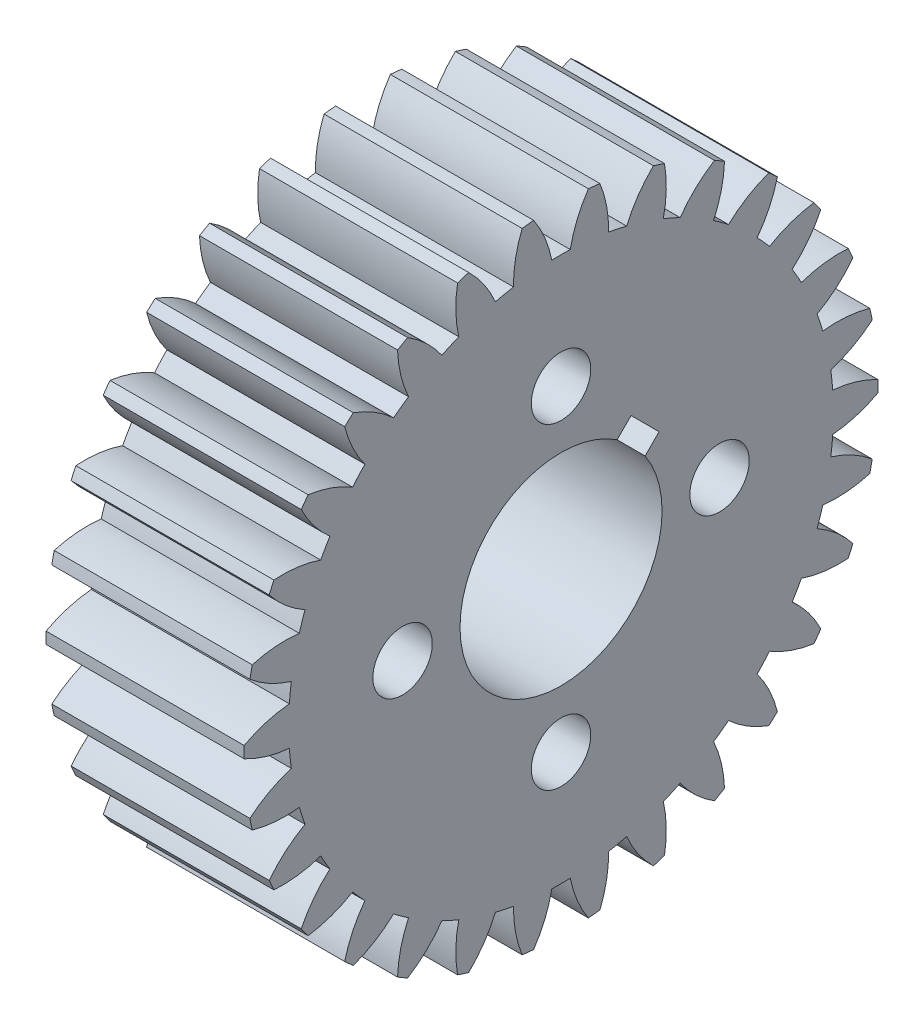
SolidWorks part; units mm, degrees
ref_plane "Plane1" through (0, 0, 0) normal (0, 0, 1) x (1, 0, 0)
ref_plane "Plane2" through (0, 0, 0) normal (0, 1, 0) x (1, 0, 0)
ref_plane "Plane3" through (0, 0, 0) normal (1, 0, 0) x (0, 0, -1)
sketch "HoldingSke" plane through (0, 0, 0) normal (0, 1, 0) x (1, 0, 0)
  line L0 (0, 0) -> (0.866, -0.5)
  line L1 (-15, 0) -> (100, 0) construction
  line L2 (0, 0) -> (-2.1039, 2.3779)
  line L3 (0, 0) -> (-11.863, 4.5341)
  line L4 (0, 0) -> (7.479, 4.318)
  line L5 (0, 0) -> (-16.8652, -6.2902)
  line L6 (0, 0) -> (-8.2896, -5.593)
  line L7 (-2.1039, 2.3779) -> (1.7706, 19.956)
  line L8 (-76.2, 54.61) -> (-75.2, 54.61)
  line L9 (-71.009, 38.7566) -> (-53.1078, 45.2721)
  line L10 (-76.2, 71.12) -> (104.1128, 71.12)
  line L11 (0, 0) -> (-10, 0)
  line L12 (-76.2, 101.6) -> (-76.162, 101.6)
  line L13 (24.9733, 27.94) -> (52.9518, 28.4284)
  line L14 (24.9733, 27.94) -> (24.9743, 27.94)
  line L15 (24.9733, 27.94) -> (100.4006, 29.5858)
  line L16 (-63.627, -1) -> (-12.827, -1)
  circle A0 centre (0, 0) radius 3
  circle A1 centre (0, 0) radius 12.5
  circle A2 centre (0, 0) radius 12.5
  circle A3 centre (0, 0) radius 3
  dimension "MHD" = 25
  dimension "Hub_dia" = 25
  dimension "Bore" = 6
  dimension "MBD" = 6
  dimension "Num_teeth" = 30
  dimension "Pitch" = 1
  dimension "Overall_len" = 18
  dimension "Show_teeth" = 30
  dimension "Thickness" = 10
  dimension "OAL" = 18.0001
  dimension "T_dim" = 1
  dimension "Ap" = 20
  dimension "H" = 19.05
  dimension "Pitch_radius" = 180.3128
  dimension "Width" = 10
  dimension "Backlash" = 0.038
  dimension "Addendum_fac" = 1
  dimension "Dedendum_fac" = 1.25
  dimension "Clearance_fac" = 0.25
  dimension "Dedendum_add" = 0.001
  dimension "Module" = 1
sketch "BasProSke" plane through (0, 0, 0) normal (0, 1, 0) x (1, 0, 0)
  line L0 (-10, 0) -> (60, 0) construction
  line L1 (0, 0) -> (0, 16)
  line L2 (0, 0) -> (10, 0)
  line L3 (10, 0) -> (10, 16)
  line L4 (10, 16) -> (0, 16)
  dimension "Thickness" = 10
  dimension "Diameter" = 32
revolve "Base-Revolve" add sketch "BasProSke" angle 360 about L0
sketch "TooCutSke" plane through (0, 0, 0) normal (1, 0, 0) x (0, 0, -1)
  line L1 (0, 0) -> (0, 107) construction
  line L2 (0, 0) -> (-0.8515, 14.9758) construction
  line L3 (0, 0) -> (-3.1323, 29.8014) construction
  line L4 (-0.8515, 14.9758) -> (-1.5661, 14.9007) construction
  arc A0 (0.4664, 13.7411) -> (-0.4664, 13.7411) centre (0, 0) ccw
  arc A1 (1.3975, 15.9644) -> (-1.3975, 15.9644) centre (0, 0) ccw
  circle A2 centre (0, 0) radius 15 construction
  circle A3 centre (0, 0) radius 14.0954 construction
  arc A4 (-0.4664, 13.7411) -> (-1.3975, 15.9644) centre (-6.3534, 12.5823) ccw
  arc A5 (1.3975, 15.9644) -> (0.4664, 13.7411) centre (6.3534, 12.5823) ccw
  dimension "Root_dia" = 27.498
  dimension "Overcut_dia" = 32.0508
  dimension "Pitch_dia" = 30
  dimension "Base_dia" = 28.1908
  dimension "Flank_rad" = 6
  dimension "Half_ang" = 6
  dimension "Half_CT" = 0.7185
extrude "ToothCut" cut sketch "TooCutSke" along normal through all
fillet "Breaks" [suppressed] radius 0.02
fillet "RootFillets" [suppressed] radius 0.251
pattern_circular "TeethCuts" count 30 every 12 about axis through (-10, 0, 0) along (1, 0, 0) of "ToothCut", "RootFillets", "Breaks"
sketch "HubNeaOneSke" plane through (0, 0, 0) normal (-1, 0, 0) x (0, 0, 1)
  circle A0 centre (0, 0) radius 12.5
  dimension "Diameter" = 25
extrude "HubNearOne" add sketch "HubNeaOneSke" along normal blind 8.0001
sketch "HubNeaBotSke" plane through (0, 0, 0) normal (-1, 0, 0) x (0, 0, 1)
  circle A0 centre (0, 0) radius 12.5
  dimension "Diameter" = 25
extrude "HubNearBoth" [suppressed] add sketch "HubNeaBotSke" along normal blind 4
ref_plane "FarPln" through (10, 0, 0) normal (1, 0, 0) x (0, 0, -1)
sketch "HubFarSke" plane through (10, 0, 0) normal (1, 0, 0) x (0, 0, -1)
  circle A0 centre (0, 0) radius 12.5
  dimension "Diameter" = 25
extrude "HubFar" [suppressed] add sketch "HubFarSke" along normal blind 4
sketch "BorSke" plane through (0, 0, 0) normal (1, 0, 0) x (0, 0, -1)
  circle A0 centre (0, 0) radius 3
  dimension "Diameter" = 6
extrude "Bore" cut sketch "BorSke" along normal mid plane 36.0001
sketch "KeySke" plane through (0, 0, 0) normal (1, 0, 0) x (0, 0, -1)
  line L0 (-1, 0) -> (-1, 4)
  line L1 (-1, 4) -> (1, 4)
  line L2 (1, 4) -> (1, 0)
  line L3 (0, 0) -> (0, 34) construction
  line L4 (-1, 0) -> (1, 0)
  dimension "Offset" = 4
  dimension "Width" = 2
extrude "Keyway" [suppressed] cut sketch "KeySke" along normal mid plane 36.0001
pattern_circular "Keyway2" [suppressed] count 2 every 90 about axis through (-10, 0, 0) along (1, 0, 0)
sketch "Sketch2" plane through (-8.0001, 0, 0) normal (-1, 0, 0) x (0, 0, 1)
  circle A1 centre (0, 0) radius 12.5
  circle A2 centre (0, 0) radius 12.5
  dimension "D1" = 0
extrude "Cut-Extrude1" cut sketch "Sketch2" against normal up to surface (8.0001 mm away) up to face at (0, 0, -12.5)
sketch "Sketch3" plane through (10, 0, 0) normal (1, 0, 0) x (0, 0, -1)
  circle A0 centre (0, 0) radius 5.1
  arc A120 (-15.9973, -0.2927) -> (-13.7146, -0.9725) centre (-13.1775, 5.0034) ccw
  arc A121 (-13.7146, -0.9725) -> (-13.6171, -1.9002) centre (0, 0) ccw
  arc A122 (-13.6171, -1.9002) -> (-15.7086, -3.0398) centre (-11.8492, -7.6338) ccw
  arc A123 (-15.7086, -3.0398) -> (-15.5869, -3.6123) centre (0, 0) ccw
  arc A124 (-15.5869, -3.6123) -> (-13.2127, -3.8027) centre (-13.9298, 2.1543) ccw
  arc A125 (-13.2127, -3.8027) -> (-12.9244, -4.6898) centre (0, 0) ccw
  arc A126 (-12.9244, -4.6898) -> (-14.7333, -6.2393) centre (-10.0031, -9.9306) ccw
  arc A127 (-14.7333, -6.2393) -> (-14.4952, -6.7741) centre (0, 0) ccw
  arc A128 (-14.4952, -6.7741) -> (-12.1333, -6.4666) centre (-14.0733, -0.7889) ccw
  arc A129 (-12.1333, -6.4666) -> (-11.6669, -7.2745) centre (0, 0) ccw
  arc A130 (-11.6669, -7.2745) -> (-13.1141, -9.1662) centre (-7.7199, -11.7934) ccw
  arc A131 (-13.1141, -9.1662) -> (-12.7701, -9.6398) centre (0, 0) ccw
  arc A132 (-12.7701, -9.6398) -> (-10.5237, -8.848) centre (-13.6017, -3.6977) ccw
  arc A133 (-10.5237, -8.848) -> (-9.8995, -9.5412) centre (0, 0) ccw
  arc A134 (-9.8995, -9.5412) -> (-10.9218, -11.6925) centre (-5.0992, -13.1407) ccw
  arc A135 (-10.9218, -11.6925) -> (-10.4868, -12.0842) centre (0, 0) ccw
  arc A136 (-10.4868, -12.0842) -> (-8.4541, -10.8426) centre (-12.5357, -6.4448) ccw
  arc A137 (-8.4541, -10.8426) -> (-7.6995, -11.3909) centre (0, 0) ccw
  arc A138 (-7.6995, -11.3909) -> (-8.2521, -13.7078) centre (-2.2556, -13.9137) ccw
  arc A139 (-8.2521, -13.7078) -> (-7.7452, -14.0004) centre (0, 0) ccw
  arc A140 (-7.7452, -14.0004) -> (-6.0151, -12.3634) centre (-10.9218, -8.9103) ccw
  arc A141 (-6.0151, -12.3634) -> (-5.1629, -12.7428) centre (0, 0) ccw
  arc A142 (-5.1629, -12.7428) -> (-5.2218, -15.1239) centre (0.6865, -14.0787) ccw
  arc A143 (-5.2218, -15.1239) -> (-4.6651, -15.3048) centre (0, 0) ccw
  arc A144 (-4.6651, -15.3048) -> (-3.3131, -13.3438) centre (-8.8306, -10.9864) ccw
  arc A145 (-3.3131, -13.3438) -> (-2.4007, -13.5378) centre (0, 0) ccw
  arc A146 (-2.4007, -13.5378) -> (-1.9632, -15.8791) centre (3.5986, -13.6283) ccw
  arc A147 (-1.9632, -15.8791) -> (-1.3811, -15.9403) centre (0, 0) ccw
  arc A148 (-1.3811, -15.9403) -> (-0.4664, -13.7411) centre (-6.3534, -12.5823) ccw
  arc A149 (-0.4664, -13.7411) -> (0.4664, -13.7411) centre (0, 0) ccw
  arc A150 (0.4664, -13.7411) -> (1.3811, -15.9403) centre (6.3534, -12.5823) ccw
  arc A151 (1.3811, -15.9403) -> (1.9632, -15.8791) centre (0, 0) ccw
  arc A152 (1.9632, -15.8791) -> (2.4007, -13.5378) centre (-3.5986, -13.6283) ccw
  arc A153 (2.4007, -13.5378) -> (3.3131, -13.3438) centre (0, 0) ccw
  arc A154 (3.3131, -13.3438) -> (4.6651, -15.3048) centre (8.8306, -10.9864) ccw
  arc A155 (4.6651, -15.3048) -> (5.2218, -15.1239) centre (0, 0) ccw
  arc A156 (5.2218, -15.1239) -> (5.1629, -12.7428) centre (-0.6865, -14.0787) ccw
  arc A157 (5.1629, -12.7428) -> (6.0151, -12.3634) centre (0, 0) ccw
  arc A158 (6.0151, -12.3634) -> (7.7452, -14.0004) centre (10.9218, -8.9103) ccw
  arc A159 (7.7452, -14.0004) -> (8.2521, -13.7078) centre (0, 0) ccw
  arc A160 (8.2521, -13.7078) -> (7.6995, -11.3909) centre (2.2556, -13.9137) ccw
  arc A161 (7.6995, -11.3909) -> (8.4541, -10.8426) centre (0, 0) ccw
  arc A162 (8.4541, -10.8426) -> (10.4868, -12.0842) centre (12.5357, -6.4448) ccw
  arc A163 (10.4868, -12.0842) -> (10.9218, -11.6925) centre (0, 0) ccw
  arc A164 (10.9218, -11.6925) -> (9.8995, -9.5412) centre (5.0992, -13.1407) ccw
  arc A165 (9.8995, -9.5412) -> (10.5237, -8.848) centre (0, 0) ccw
  arc A166 (10.5237, -8.848) -> (12.7701, -9.6398) centre (13.6017, -3.6977) ccw
  arc A167 (12.7701, -9.6398) -> (13.1141, -9.1662) centre (0, 0) ccw
  arc A168 (13.1141, -9.1662) -> (11.6669, -7.2745) centre (7.7199, -11.7934) ccw
  arc A169 (11.6669, -7.2745) -> (12.1333, -6.4666) centre (0, 0) ccw
  arc A170 (12.1333, -6.4666) -> (14.4952, -6.7741) centre (14.0733, -0.7889) ccw
  arc A171 (14.4952, -6.7741) -> (14.7333, -6.2393) centre (0, 0) ccw
  arc A172 (14.7333, -6.2393) -> (12.9244, -4.6898) centre (10.0031, -9.9306) ccw
  arc A173 (12.9244, -4.6898) -> (13.2127, -3.8027) centre (0, 0) ccw
  arc A174 (13.2127, -3.8027) -> (15.5869, -3.6123) centre (13.9298, 2.1543) ccw
  arc A175 (15.5869, -3.6123) -> (15.7086, -3.0398) centre (0, 0) ccw
  arc A176 (15.7086, -3.0398) -> (13.6171, -1.9002) centre (11.8492, -7.6338) ccw
  arc A177 (13.6171, -1.9002) -> (13.7146, -0.9725) centre (0, 0) ccw
  arc A178 (13.7146, -0.9725) -> (15.9973, -0.2927) centre (13.1775, 5.0034) ccw
  arc A179 (15.9973, -0.2927) -> (15.9973, 0.2927) centre (0, 0) ccw
  arc A180 (15.9973, 0.2927) -> (13.7146, 0.9725) centre (13.1775, -5.0034) ccw
  arc A181 (13.7146, 0.9725) -> (13.6171, 1.9002) centre (0, 0) ccw
  arc A182 (13.6171, 1.9002) -> (15.7086, 3.0398) centre (11.8492, 7.6338) ccw
  arc A183 (15.7086, 3.0398) -> (15.5869, 3.6123) centre (0, 0) ccw
  arc A184 (15.5869, 3.6123) -> (13.2127, 3.8027) centre (13.9298, -2.1543) ccw
  arc A185 (13.2127, 3.8027) -> (12.9244, 4.6898) centre (0, 0) ccw
  arc A186 (12.9244, 4.6898) -> (14.7333, 6.2393) centre (10.0031, 9.9306) ccw
  arc A187 (14.7333, 6.2393) -> (14.4952, 6.7741) centre (0, 0) ccw
  arc A188 (14.4952, 6.7741) -> (12.1333, 6.4666) centre (14.0733, 0.7889) ccw
  arc A189 (12.1333, 6.4666) -> (11.6669, 7.2745) centre (0, 0) ccw
  arc A190 (11.6669, 7.2745) -> (13.1141, 9.1662) centre (7.7199, 11.7934) ccw
  arc A191 (13.1141, 9.1662) -> (12.7701, 9.6398) centre (0, 0) ccw
  arc A192 (12.7701, 9.6398) -> (10.5237, 8.848) centre (13.6017, 3.6977) ccw
  arc A193 (10.5237, 8.848) -> (9.8995, 9.5412) centre (0, 0) ccw
  arc A194 (9.8995, 9.5412) -> (10.9218, 11.6925) centre (5.0992, 13.1407) ccw
  arc A195 (10.9218, 11.6925) -> (10.4868, 12.0842) centre (0, 0) ccw
  arc A196 (10.4868, 12.0842) -> (8.4541, 10.8426) centre (12.5357, 6.4448) ccw
  arc A197 (8.4541, 10.8426) -> (7.6995, 11.3909) centre (0, 0) ccw
  arc A198 (7.6995, 11.3909) -> (8.2521, 13.7078) centre (2.2556, 13.9137) ccw
  arc A199 (8.2521, 13.7078) -> (7.7452, 14.0004) centre (0, 0) ccw
  arc A200 (7.7452, 14.0004) -> (6.0151, 12.3634) centre (10.9218, 8.9103) ccw
  arc A201 (6.0151, 12.3634) -> (5.1629, 12.7428) centre (0, 0) ccw
  arc A202 (5.1629, 12.7428) -> (5.2218, 15.1239) centre (-0.6865, 14.0787) ccw
  arc A203 (5.2218, 15.1239) -> (4.6651, 15.3048) centre (0, 0) ccw
  arc A204 (4.6651, 15.3048) -> (3.3131, 13.3438) centre (8.8306, 10.9864) ccw
  arc A205 (3.3131, 13.3438) -> (2.4007, 13.5378) centre (0, 0) ccw
  arc A206 (2.4007, 13.5378) -> (1.9632, 15.8791) centre (-3.5986, 13.6283) ccw
  arc A207 (1.9632, 15.8791) -> (1.3811, 15.9403) centre (0, 0) ccw
  arc A208 (1.3811, 15.9403) -> (0.4664, 13.7411) centre (6.3534, 12.5823) ccw
  arc A209 (0.4664, 13.7411) -> (-0.4664, 13.7411) centre (0, 0) ccw
  arc A210 (-0.4664, 13.7411) -> (-1.3811, 15.9403) centre (-6.3534, 12.5823) ccw
  arc A211 (-1.3811, 15.9403) -> (-1.9632, 15.8791) centre (0, 0) ccw
  arc A212 (-1.9632, 15.8791) -> (-2.4007, 13.5378) centre (3.5986, 13.6283) ccw
  arc A213 (-2.4007, 13.5378) -> (-3.3131, 13.3438) centre (0, 0) ccw
  arc A214 (-3.3131, 13.3438) -> (-4.6651, 15.3048) centre (-8.8306, 10.9864) ccw
  arc A215 (-4.6651, 15.3048) -> (-5.2218, 15.1239) centre (0, 0) ccw
  arc A216 (-5.2218, 15.1239) -> (-5.1629, 12.7428) centre (0.6865, 14.0787) ccw
  arc A217 (-5.1629, 12.7428) -> (-6.0151, 12.3634) centre (0, 0) ccw
  arc A218 (-6.0151, 12.3634) -> (-7.7452, 14.0004) centre (-10.9218, 8.9103) ccw
  arc A219 (-7.7452, 14.0004) -> (-8.2521, 13.7078) centre (0, 0) ccw
  arc A220 (-8.2521, 13.7078) -> (-7.6995, 11.3909) centre (-2.2556, 13.9137) ccw
  arc A221 (-7.6995, 11.3909) -> (-8.4541, 10.8426) centre (0, 0) ccw
  arc A222 (-8.4541, 10.8426) -> (-10.4868, 12.0842) centre (-12.5357, 6.4448) ccw
  arc A223 (-10.4868, 12.0842) -> (-10.9218, 11.6925) centre (0, 0) ccw
  arc A224 (-10.9218, 11.6925) -> (-9.8995, 9.5412) centre (-5.0992, 13.1407) ccw
  arc A225 (-9.8995, 9.5412) -> (-10.5237, 8.848) centre (0, 0) ccw
  arc A226 (-10.5237, 8.848) -> (-12.7701, 9.6398) centre (-13.6017, 3.6977) ccw
  arc A227 (-12.7701, 9.6398) -> (-13.1141, 9.1662) centre (0, 0) ccw
  arc A228 (-13.1141, 9.1662) -> (-11.6669, 7.2745) centre (-7.7199, 11.7934) ccw
  arc A229 (-11.6669, 7.2745) -> (-12.1333, 6.4666) centre (0, 0) ccw
  arc A230 (-12.1333, 6.4666) -> (-14.4952, 6.7741) centre (-14.0733, 0.7889) ccw
  arc A231 (-14.4952, 6.7741) -> (-14.7333, 6.2393) centre (0, 0) ccw
  arc A232 (-14.7333, 6.2393) -> (-12.9244, 4.6898) centre (-10.0031, 9.9306) ccw
  arc A233 (-12.9244, 4.6898) -> (-13.2127, 3.8027) centre (0, 0) ccw
  arc A234 (-13.2127, 3.8027) -> (-15.5869, 3.6123) centre (-13.9298, -2.1543) ccw
  arc A235 (-15.5869, 3.6123) -> (-15.7086, 3.0398) centre (0, 0) ccw
  arc A236 (-15.7086, 3.0398) -> (-13.6171, 1.9002) centre (-11.8492, 7.6338) ccw
  arc A237 (-13.6171, 1.9002) -> (-13.7146, 0.9725) centre (0, 0) ccw
  arc A238 (-13.7146, 0.9725) -> (-15.9973, 0.2927) centre (-13.1775, -5.0034) ccw
  arc A239 (-15.9973, 0.2927) -> (-15.9973, -0.2927) centre (0, 0) ccw
  arc A240 (-15.9973, -0.2927) -> (-13.7146, -0.9725) centre (-13.1775, 5.0034) ccw
  arc A241 (-13.7146, -0.9725) -> (-13.6171, -1.9002) centre (0, 0) ccw
  arc A242 (-13.6171, -1.9002) -> (-15.7086, -3.0398) centre (-11.8492, -7.6338) ccw
  arc A243 (-15.7086, -3.0398) -> (-15.5869, -3.6123) centre (0, 0) ccw
  arc A244 (-15.5869, -3.6123) -> (-13.2127, -3.8027) centre (-13.9298, 2.1543) ccw
  arc A245 (-13.2127, -3.8027) -> (-12.9244, -4.6898) centre (0, 0) ccw
  arc A246 (-12.9244, -4.6898) -> (-14.7333, -6.2393) centre (-10.0031, -9.9306) ccw
  arc A247 (-14.7333, -6.2393) -> (-14.4952, -6.7741) centre (0, 0) ccw
  arc A248 (-14.4952, -6.7741) -> (-12.1333, -6.4666) centre (-14.0733, -0.7889) ccw
  arc A249 (-12.1333, -6.4666) -> (-11.6669, -7.2745) centre (0, 0) ccw
  arc A250 (-11.6669, -7.2745) -> (-13.1141, -9.1662) centre (-7.7199, -11.7934) ccw
  arc A251 (-13.1141, -9.1662) -> (-12.7701, -9.6398) centre (0, 0) ccw
  arc A252 (-12.7701, -9.6398) -> (-10.5237, -8.848) centre (-13.6017, -3.6977) ccw
  arc A253 (-10.5237, -8.848) -> (-9.8995, -9.5412) centre (0, 0) ccw
  arc A254 (-9.8995, -9.5412) -> (-10.9218, -11.6925) centre (-5.0992, -13.1407) ccw
  arc A255 (-10.9218, -11.6925) -> (-10.4868, -12.0842) centre (0, 0) ccw
  arc A256 (-10.4868, -12.0842) -> (-8.4541, -10.8426) centre (-12.5357, -6.4448) ccw
  arc A257 (-8.4541, -10.8426) -> (-7.6995, -11.3909) centre (0, 0) ccw
  arc A258 (-7.6995, -11.3909) -> (-8.2521, -13.7078) centre (-2.2556, -13.9137) ccw
  arc A259 (-8.2521, -13.7078) -> (-7.7452, -14.0004) centre (0, 0) ccw
  arc A260 (-7.7452, -14.0004) -> (-6.0151, -12.3634) centre (-10.9218, -8.9103) ccw
  arc A261 (-6.0151, -12.3634) -> (-5.1629, -12.7428) centre (0, 0) ccw
  arc A262 (-5.1629, -12.7428) -> (-5.2218, -15.1239) centre (0.6865, -14.0787) ccw
  arc A263 (-5.2218, -15.1239) -> (-4.6651, -15.3048) centre (0, 0) ccw
  arc A264 (-4.6651, -15.3048) -> (-3.3131, -13.3438) centre (-8.8306, -10.9864) ccw
  arc A265 (-3.3131, -13.3438) -> (-2.4007, -13.5378) centre (0, 0) ccw
  arc A266 (-2.4007, -13.5378) -> (-1.9632, -15.8791) centre (3.5986, -13.6283) ccw
  arc A267 (-1.9632, -15.8791) -> (-1.3811, -15.9403) centre (0, 0) ccw
  arc A268 (-1.3811, -15.9403) -> (-0.4664, -13.7411) centre (-6.3534, -12.5823) ccw
  arc A269 (-0.4664, -13.7411) -> (0.4664, -13.7411) centre (0, 0) ccw
  arc A270 (0.4664, -13.7411) -> (1.3811, -15.9403) centre (6.3534, -12.5823) ccw
  arc A271 (1.3811, -15.9403) -> (1.9632, -15.8791) centre (0, 0) ccw
  arc A272 (1.9632, -15.8791) -> (2.4007, -13.5378) centre (-3.5986, -13.6283) ccw
  arc A273 (2.4007, -13.5378) -> (3.3131, -13.3438) centre (0, 0) ccw
  arc A274 (3.3131, -13.3438) -> (4.6651, -15.3048) centre (8.8306, -10.9864) ccw
  arc A275 (4.6651, -15.3048) -> (5.2218, -15.1239) centre (0, 0) ccw
  arc A276 (5.2218, -15.1239) -> (5.1629, -12.7428) centre (-0.6865, -14.0787) ccw
  arc A277 (5.1629, -12.7428) -> (6.0151, -12.3634) centre (0, 0) ccw
  arc A278 (6.0151, -12.3634) -> (7.7452, -14.0004) centre (10.9218, -8.9103) ccw
  arc A279 (7.7452, -14.0004) -> (8.2521, -13.7078) centre (0, 0) ccw
  arc A280 (8.2521, -13.7078) -> (7.6995, -11.3909) centre (2.2556, -13.9137) ccw
  arc A281 (7.6995, -11.3909) -> (8.4541, -10.8426) centre (0, 0) ccw
  arc A282 (8.4541, -10.8426) -> (10.4868, -12.0842) centre (12.5357, -6.4448) ccw
  arc A283 (10.4868, -12.0842) -> (10.9218, -11.6925) centre (0, 0) ccw
  arc A284 (10.9218, -11.6925) -> (9.8995, -9.5412) centre (5.0992, -13.1407) ccw
  arc A285 (9.8995, -9.5412) -> (10.5237, -8.848) centre (0, 0) ccw
  arc A286 (10.5237, -8.848) -> (12.7701, -9.6398) centre (13.6017, -3.6977) ccw
  arc A287 (12.7701, -9.6398) -> (13.1141, -9.1662) centre (0, 0) ccw
  arc A288 (13.1141, -9.1662) -> (11.6669, -7.2745) centre (7.7199, -11.7934) ccw
  arc A289 (11.6669, -7.2745) -> (12.1333, -6.4666) centre (0, 0) ccw
  arc A290 (12.1333, -6.4666) -> (14.4952, -6.7741) centre (14.0733, -0.7889) ccw
  arc A291 (14.4952, -6.7741) -> (14.7333, -6.2393) centre (0, 0) ccw
  arc A292 (14.7333, -6.2393) -> (12.9244, -4.6898) centre (10.0031, -9.9306) ccw
  arc A293 (12.9244, -4.6898) -> (13.2127, -3.8027) centre (0, 0) ccw
  arc A294 (13.2127, -3.8027) -> (15.5869, -3.6123) centre (13.9298, 2.1543) ccw
  arc A295 (15.5869, -3.6123) -> (15.7086, -3.0398) centre (0, 0) ccw
  arc A296 (15.7086, -3.0398) -> (13.6171, -1.9002) centre (11.8492, -7.6338) ccw
  arc A297 (13.6171, -1.9002) -> (13.7146, -0.9725) centre (0, 0) ccw
  arc A298 (13.7146, -0.9725) -> (15.9973, -0.2927) centre (13.1775, 5.0034) ccw
  arc A299 (15.9973, -0.2927) -> (15.9973, 0.2927) centre (0, 0) ccw
  arc A300 (15.9973, 0.2927) -> (13.7146, 0.9725) centre (13.1775, -5.0034) ccw
  arc A301 (13.7146, 0.9725) -> (13.6171, 1.9002) centre (0, 0) ccw
  arc A302 (13.6171, 1.9002) -> (15.7086, 3.0398) centre (11.8492, 7.6338) ccw
  arc A303 (15.7086, 3.0398) -> (15.5869, 3.6123) centre (0, 0) ccw
  arc A304 (15.5869, 3.6123) -> (13.2127, 3.8027) centre (13.9298, -2.1543) ccw
  arc A305 (13.2127, 3.8027) -> (12.9244, 4.6898) centre (0, 0) ccw
  arc A306 (12.9244, 4.6898) -> (14.7333, 6.2393) centre (10.0031, 9.9306) ccw
  arc A307 (14.7333, 6.2393) -> (14.4952, 6.7741) centre (0, 0) ccw
  arc A308 (14.4952, 6.7741) -> (12.1333, 6.4666) centre (14.0733, 0.7889) ccw
  arc A309 (12.1333, 6.4666) -> (11.6669, 7.2745) centre (0, 0) ccw
  arc A310 (11.6669, 7.2745) -> (13.1141, 9.1662) centre (7.7199, 11.7934) ccw
  arc A311 (13.1141, 9.1662) -> (12.7701, 9.6398) centre (0, 0) ccw
  arc A312 (12.7701, 9.6398) -> (10.5237, 8.848) centre (13.6017, 3.6977) ccw
  arc A313 (10.5237, 8.848) -> (9.8995, 9.5412) centre (0, 0) ccw
  arc A314 (9.8995, 9.5412) -> (10.9218, 11.6925) centre (5.0992, 13.1407) ccw
  arc A315 (10.9218, 11.6925) -> (10.4868, 12.0842) centre (0, 0) ccw
  arc A316 (10.4868, 12.0842) -> (8.4541, 10.8426) centre (12.5357, 6.4448) ccw
  arc A317 (8.4541, 10.8426) -> (7.6995, 11.3909) centre (0, 0) ccw
  arc A318 (7.6995, 11.3909) -> (8.2521, 13.7078) centre (2.2556, 13.9137) ccw
  arc A319 (8.2521, 13.7078) -> (7.7452, 14.0004) centre (0, 0) ccw
  arc A320 (7.7452, 14.0004) -> (6.0151, 12.3634) centre (10.9218, 8.9103) ccw
  arc A321 (6.0151, 12.3634) -> (5.1629, 12.7428) centre (0, 0) ccw
  arc A322 (5.1629, 12.7428) -> (5.2218, 15.1239) centre (-0.6865, 14.0787) ccw
  arc A323 (5.2218, 15.1239) -> (4.6651, 15.3048) centre (0, 0) ccw
  arc A324 (4.6651, 15.3048) -> (3.3131, 13.3438) centre (8.8306, 10.9864) ccw
  arc A325 (3.3131, 13.3438) -> (2.4007, 13.5378) centre (0, 0) ccw
  arc A326 (2.4007, 13.5378) -> (1.9632, 15.8791) centre (-3.5986, 13.6283) ccw
  arc A327 (1.9632, 15.8791) -> (1.3811, 15.9403) centre (0, 0) ccw
  arc A328 (1.3811, 15.9403) -> (0.4664, 13.7411) centre (6.3534, 12.5823) ccw
  arc A329 (0.4664, 13.7411) -> (-0.4664, 13.7411) centre (0, 0) ccw
  arc A330 (-0.4664, 13.7411) -> (-1.3811, 15.9403) centre (-6.3534, 12.5823) ccw
  arc A331 (-1.3811, 15.9403) -> (-1.9632, 15.8791) centre (0, 0) ccw
  arc A332 (-1.9632, 15.8791) -> (-2.4007, 13.5378) centre (3.5986, 13.6283) ccw
  arc A333 (-2.4007, 13.5378) -> (-3.3131, 13.3438) centre (0, 0) ccw
  arc A334 (-3.3131, 13.3438) -> (-4.6651, 15.3048) centre (-8.8306, 10.9864) ccw
  arc A335 (-4.6651, 15.3048) -> (-5.2218, 15.1239) centre (0, 0) ccw
  arc A336 (-5.2218, 15.1239) -> (-5.1629, 12.7428) centre (0.6865, 14.0787) ccw
  arc A337 (-5.1629, 12.7428) -> (-6.0151, 12.3634) centre (0, 0) ccw
  arc A338 (-6.0151, 12.3634) -> (-7.7452, 14.0004) centre (-10.9218, 8.9103) ccw
  arc A339 (-7.7452, 14.0004) -> (-8.2521, 13.7078) centre (0, 0) ccw
  arc A340 (-8.2521, 13.7078) -> (-7.6995, 11.3909) centre (-2.2556, 13.9137) ccw
  arc A341 (-7.6995, 11.3909) -> (-8.4541, 10.8426) centre (0, 0) ccw
  arc A342 (-8.4541, 10.8426) -> (-10.4868, 12.0842) centre (-12.5357, 6.4448) ccw
  arc A343 (-10.4868, 12.0842) -> (-10.9218, 11.6925) centre (0, 0) ccw
  arc A344 (-10.9218, 11.6925) -> (-9.8995, 9.5412) centre (-5.0992, 13.1407) ccw
  arc A345 (-9.8995, 9.5412) -> (-10.5237, 8.848) centre (0, 0) ccw
  arc A346 (-10.5237, 8.848) -> (-12.7701, 9.6398) centre (-13.6017, 3.6977) ccw
  arc A347 (-12.7701, 9.6398) -> (-13.1141, 9.1662) centre (0, 0) ccw
  arc A348 (-13.1141, 9.1662) -> (-11.6669, 7.2745) centre (-7.7199, 11.7934) ccw
  arc A349 (-11.6669, 7.2745) -> (-12.1333, 6.4666) centre (0, 0) ccw
  arc A350 (-12.1333, 6.4666) -> (-14.4952, 6.7741) centre (-14.0733, 0.7889) ccw
  arc A351 (-14.4952, 6.7741) -> (-14.7333, 6.2393) centre (0, 0) ccw
  arc A352 (-14.7333, 6.2393) -> (-12.9244, 4.6898) centre (-10.0031, 9.9306) ccw
  arc A353 (-12.9244, 4.6898) -> (-13.2127, 3.8027) centre (0, 0) ccw
  arc A354 (-13.2127, 3.8027) -> (-15.5869, 3.6123) centre (-13.9298, -2.1543) ccw
  arc A355 (-15.5869, 3.6123) -> (-15.7086, 3.0398) centre (0, 0) ccw
  arc A356 (-15.7086, 3.0398) -> (-13.6171, 1.9002) centre (-11.8492, 7.6338) ccw
  arc A357 (-13.6171, 1.9002) -> (-13.7146, 0.9725) centre (0, 0) ccw
  arc A358 (-13.7146, 0.9725) -> (-15.9973, 0.2927) centre (-13.1775, -5.0034) ccw
  arc A359 (-15.9973, 0.2927) -> (-15.9973, -0.2927) centre (0, 0) ccw
  dimension "D2" = 10.2
  dimension "D1" = 0
extrude "Cut-Extrude2" cut sketch "Sketch3" against normal blind 10 contours A0
sketch "Sketch4" plane through (0, 0, 0) normal (-1, 0, 0) x (0, 0, 1)
  line L0 (0, 0) -> (0, -8)
  line L1 (0, 0) -> (-5.6569, 5.6569)
  line L2 (1, 0.4142) -> (1, -8)
  line L3 (1, 0.4142) -> (-4.9497, 6.364)
  line L4 (-1, -0.4142) -> (-1, -8)
  line L5 (-1, -0.4142) -> (-6.364, 4.9497)
  line L6 (-4.9497, 3.5355) -> (-3.5355, 4.9497)
  circle A0 centre (0, 0) radius 8
  circle A1 centre (0, -8) radius 1.5
  circle A2 centre (-8, 0) radius 1.5
  circle A3 centre (0, 8) radius 1.5
  circle A4 centre (8, 0) radius 1.5
  circle A5 centre (0, 0) radius 5.1
  arc A125 (13.7146, -0.9725) -> (15.9973, -0.2927) centre (13.1775, 5.0034) ccw
  arc A126 (15.9973, -0.2927) -> (15.9973, 0.2927) centre (0, 0) ccw
  arc A127 (15.9973, 0.2927) -> (13.7146, 0.9725) centre (13.1775, -5.0034) ccw
  arc A128 (13.7146, 0.9725) -> (13.6171, 1.9002) centre (0, 0) ccw
  arc A129 (13.6171, 1.9002) -> (15.7086, 3.0398) centre (11.8492, 7.6338) ccw
  arc A130 (15.7086, 3.0398) -> (15.5869, 3.6123) centre (0, 0) ccw
  arc A131 (15.5869, 3.6123) -> (13.2127, 3.8027) centre (13.9298, -2.1543) ccw
  arc A132 (13.2127, 3.8027) -> (12.9244, 4.6898) centre (0, 0) ccw
  arc A133 (12.9244, 4.6898) -> (14.7333, 6.2393) centre (10.0031, 9.9306) ccw
  arc A134 (14.7333, 6.2393) -> (14.4952, 6.7741) centre (0, 0) ccw
  arc A135 (14.4952, 6.7741) -> (12.1333, 6.4666) centre (14.0733, 0.7889) ccw
  arc A136 (12.1333, 6.4666) -> (11.6669, 7.2745) centre (0, 0) ccw
  arc A137 (11.6669, 7.2745) -> (13.1141, 9.1662) centre (7.7199, 11.7934) ccw
  arc A138 (13.1141, 9.1662) -> (12.7701, 9.6398) centre (0, 0) ccw
  arc A139 (12.7701, 9.6398) -> (10.5237, 8.848) centre (13.6017, 3.6977) ccw
  arc A140 (10.5237, 8.848) -> (9.8995, 9.5412) centre (0, 0) ccw
  arc A141 (9.8995, 9.5412) -> (10.9218, 11.6925) centre (5.0992, 13.1407) ccw
  arc A142 (10.9218, 11.6925) -> (10.4868, 12.0842) centre (0, 0) ccw
  arc A143 (10.4868, 12.0842) -> (8.4541, 10.8426) centre (12.5357, 6.4448) ccw
  arc A144 (8.4541, 10.8426) -> (7.6995, 11.3909) centre (0, 0) ccw
  arc A145 (7.6995, 11.3909) -> (8.2521, 13.7078) centre (2.2556, 13.9137) ccw
  arc A146 (8.2521, 13.7078) -> (7.7452, 14.0004) centre (0, 0) ccw
  arc A147 (7.7452, 14.0004) -> (6.0151, 12.3634) centre (10.9218, 8.9103) ccw
  arc A148 (6.0151, 12.3634) -> (5.1629, 12.7428) centre (0, 0) ccw
  arc A149 (5.1629, 12.7428) -> (5.2218, 15.1239) centre (-0.6865, 14.0787) ccw
  arc A150 (5.2218, 15.1239) -> (4.6651, 15.3048) centre (0, 0) ccw
  arc A151 (4.6651, 15.3048) -> (3.3131, 13.3438) centre (8.8306, 10.9864) ccw
  arc A152 (3.3131, 13.3438) -> (2.4007, 13.5378) centre (0, 0) ccw
  arc A153 (2.4007, 13.5378) -> (1.9632, 15.8791) centre (-3.5986, 13.6283) ccw
  arc A154 (1.9632, 15.8791) -> (1.3811, 15.9403) centre (0, 0) ccw
  arc A155 (1.3811, 15.9403) -> (0.4664, 13.7411) centre (6.3534, 12.5823) ccw
  arc A156 (0.4664, 13.7411) -> (-0.4664, 13.7411) centre (0, 0) ccw
  arc A157 (-0.4664, 13.7411) -> (-1.3811, 15.9403) centre (-6.3534, 12.5823) ccw
  arc A158 (-1.3811, 15.9403) -> (-1.9632, 15.8791) centre (0, 0) ccw
  arc A159 (-1.9632, 15.8791) -> (-2.4007, 13.5378) centre (3.5986, 13.6283) ccw
  arc A160 (-2.4007, 13.5378) -> (-3.3131, 13.3438) centre (0, 0) ccw
  arc A161 (-3.3131, 13.3438) -> (-4.6651, 15.3048) centre (-8.8306, 10.9864) ccw
  arc A162 (-4.6651, 15.3048) -> (-5.2218, 15.1239) centre (0, 0) ccw
  arc A163 (-5.2218, 15.1239) -> (-5.1629, 12.7428) centre (0.6865, 14.0787) ccw
  arc A164 (-5.1629, 12.7428) -> (-6.0151, 12.3634) centre (0, 0) ccw
  arc A165 (-6.0151, 12.3634) -> (-7.7452, 14.0004) centre (-10.9218, 8.9103) ccw
  arc A166 (-7.7452, 14.0004) -> (-8.2521, 13.7078) centre (0, 0) ccw
  arc A167 (-8.2521, 13.7078) -> (-7.6995, 11.3909) centre (-2.2556, 13.9137) ccw
  arc A168 (-7.6995, 11.3909) -> (-8.4541, 10.8426) centre (0, 0) ccw
  arc A169 (-8.4541, 10.8426) -> (-10.4868, 12.0842) centre (-12.5357, 6.4448) ccw
  arc A170 (-10.4868, 12.0842) -> (-10.9218, 11.6925) centre (0, 0) ccw
  arc A171 (-10.9218, 11.6925) -> (-9.8995, 9.5412) centre (-5.0992, 13.1407) ccw
  arc A172 (-9.8995, 9.5412) -> (-10.5237, 8.848) centre (0, 0) ccw
  arc A173 (-10.5237, 8.848) -> (-12.7701, 9.6398) centre (-13.6017, 3.6977) ccw
  arc A174 (-12.7701, 9.6398) -> (-13.1141, 9.1662) centre (0, 0) ccw
  arc A175 (-13.1141, 9.1662) -> (-11.6669, 7.2745) centre (-7.7199, 11.7934) ccw
  arc A176 (-11.6669, 7.2745) -> (-12.1333, 6.4666) centre (0, 0) ccw
  arc A177 (-12.1333, 6.4666) -> (-14.4952, 6.7741) centre (-14.0733, 0.7889) ccw
  arc A178 (-14.4952, 6.7741) -> (-14.7333, 6.2393) centre (0, 0) ccw
  arc A179 (-14.7333, 6.2393) -> (-12.9244, 4.6898) centre (-10.0031, 9.9306) ccw
  arc A180 (-12.9244, 4.6898) -> (-13.2127, 3.8027) centre (0, 0) ccw
  arc A181 (-13.2127, 3.8027) -> (-15.5869, 3.6123) centre (-13.9298, -2.1543) ccw
  arc A182 (-15.5869, 3.6123) -> (-15.7086, 3.0398) centre (0, 0) ccw
  arc A183 (-15.7086, 3.0398) -> (-13.6171, 1.9002) centre (-11.8492, 7.6338) ccw
  arc A184 (-13.6171, 1.9002) -> (-13.7146, 0.9725) centre (0, 0) ccw
  arc A185 (-13.7146, 0.9725) -> (-15.9973, 0.2927) centre (-13.1775, -5.0034) ccw
  arc A186 (-15.9973, 0.2927) -> (-15.9973, -0.2927) centre (0, 0) ccw
  arc A187 (-15.9973, -0.2927) -> (-13.7146, -0.9725) centre (-13.1775, 5.0034) ccw
  arc A188 (-13.7146, -0.9725) -> (-13.6171, -1.9002) centre (0, 0) ccw
  arc A189 (-13.6171, -1.9002) -> (-15.7086, -3.0398) centre (-11.8492, -7.6338) ccw
  arc A190 (-15.7086, -3.0398) -> (-15.5869, -3.6123) centre (0, 0) ccw
  arc A191 (-15.5869, -3.6123) -> (-13.2127, -3.8027) centre (-13.9298, 2.1543) ccw
  arc A192 (-13.2127, -3.8027) -> (-12.9244, -4.6898) centre (0, 0) ccw
  arc A193 (-12.9244, -4.6898) -> (-14.7333, -6.2393) centre (-10.0031, -9.9306) ccw
  arc A194 (-14.7333, -6.2393) -> (-14.4952, -6.7741) centre (0, 0) ccw
  arc A195 (-14.4952, -6.7741) -> (-12.1333, -6.4666) centre (-14.0733, -0.7889) ccw
  arc A196 (-12.1333, -6.4666) -> (-11.6669, -7.2745) centre (0, 0) ccw
  arc A197 (-11.6669, -7.2745) -> (-13.1141, -9.1662) centre (-7.7199, -11.7934) ccw
  arc A198 (-13.1141, -9.1662) -> (-12.7701, -9.6398) centre (0, 0) ccw
  arc A199 (-12.7701, -9.6398) -> (-10.5237, -8.848) centre (-13.6017, -3.6977) ccw
  arc A200 (-10.5237, -8.848) -> (-9.8995, -9.5412) centre (0, 0) ccw
  arc A201 (-9.8995, -9.5412) -> (-10.9218, -11.6925) centre (-5.0992, -13.1407) ccw
  arc A202 (-10.9218, -11.6925) -> (-10.4868, -12.0842) centre (0, 0) ccw
  arc A203 (-10.4868, -12.0842) -> (-8.4541, -10.8426) centre (-12.5357, -6.4448) ccw
  arc A204 (-8.4541, -10.8426) -> (-7.6995, -11.3909) centre (0, 0) ccw
  arc A205 (-7.6995, -11.3909) -> (-8.2521, -13.7078) centre (-2.2556, -13.9137) ccw
  arc A206 (-8.2521, -13.7078) -> (-7.7452, -14.0004) centre (0, 0) ccw
  arc A207 (-7.7452, -14.0004) -> (-6.0151, -12.3634) centre (-10.9218, -8.9103) ccw
  arc A208 (-6.0151, -12.3634) -> (-5.1629, -12.7428) centre (0, 0) ccw
  arc A209 (-5.1629, -12.7428) -> (-5.2218, -15.1239) centre (0.6865, -14.0787) ccw
  arc A210 (-5.2218, -15.1239) -> (-4.6651, -15.3048) centre (0, 0) ccw
  arc A211 (-4.6651, -15.3048) -> (-3.3131, -13.3438) centre (-8.8306, -10.9864) ccw
  arc A212 (-3.3131, -13.3438) -> (-2.4007, -13.5378) centre (0, 0) ccw
  arc A213 (-2.4007, -13.5378) -> (-1.9632, -15.8791) centre (3.5986, -13.6283) ccw
  arc A214 (-1.9632, -15.8791) -> (-1.3811, -15.9403) centre (0, 0) ccw
  arc A215 (-1.3811, -15.9403) -> (-0.4664, -13.7411) centre (-6.3534, -12.5823) ccw
  arc A216 (-0.4664, -13.7411) -> (0.4664, -13.7411) centre (0, 0) ccw
  arc A217 (0.4664, -13.7411) -> (1.3811, -15.9403) centre (6.3534, -12.5823) ccw
  arc A218 (1.3811, -15.9403) -> (1.9632, -15.8791) centre (0, 0) ccw
  arc A219 (1.9632, -15.8791) -> (2.4007, -13.5378) centre (-3.5986, -13.6283) ccw
  arc A220 (2.4007, -13.5378) -> (3.3131, -13.3438) centre (0, 0) ccw
  arc A221 (3.3131, -13.3438) -> (4.6651, -15.3048) centre (8.8306, -10.9864) ccw
  arc A222 (4.6651, -15.3048) -> (5.2218, -15.1239) centre (0, 0) ccw
  arc A223 (5.2218, -15.1239) -> (5.1629, -12.7428) centre (-0.6865, -14.0787) ccw
  arc A224 (5.1629, -12.7428) -> (6.0151, -12.3634) centre (0, 0) ccw
  arc A225 (6.0151, -12.3634) -> (7.7452, -14.0004) centre (10.9218, -8.9103) ccw
  arc A226 (7.7452, -14.0004) -> (8.2521, -13.7078) centre (0, 0) ccw
  arc A227 (8.2521, -13.7078) -> (7.6995, -11.3909) centre (2.2556, -13.9137) ccw
  arc A228 (7.6995, -11.3909) -> (8.4541, -10.8426) centre (0, 0) ccw
  arc A229 (8.4541, -10.8426) -> (10.4868, -12.0842) centre (12.5357, -6.4448) ccw
  arc A230 (10.4868, -12.0842) -> (10.9218, -11.6925) centre (0, 0) ccw
  arc A231 (10.9218, -11.6925) -> (9.8995, -9.5412) centre (5.0992, -13.1407) ccw
  arc A232 (9.8995, -9.5412) -> (10.5237, -8.848) centre (0, 0) ccw
  arc A233 (10.5237, -8.848) -> (12.7701, -9.6398) centre (13.6017, -3.6977) ccw
  arc A234 (12.7701, -9.6398) -> (13.1141, -9.1662) centre (0, 0) ccw
  arc A235 (13.1141, -9.1662) -> (11.6669, -7.2745) centre (7.7199, -11.7934) ccw
  arc A236 (11.6669, -7.2745) -> (12.1333, -6.4666) centre (0, 0) ccw
  arc A237 (12.1333, -6.4666) -> (14.4952, -6.7741) centre (14.0733, -0.7889) ccw
  arc A238 (14.4952, -6.7741) -> (14.7333, -6.2393) centre (0, 0) ccw
  arc A239 (14.7333, -6.2393) -> (12.9244, -4.6898) centre (10.0031, -9.9306) ccw
  arc A240 (12.9244, -4.6898) -> (13.2127, -3.8027) centre (0, 0) ccw
  arc A241 (13.2127, -3.8027) -> (15.5869, -3.6123) centre (13.9298, 2.1543) ccw
  arc A242 (15.5869, -3.6123) -> (15.7086, -3.0398) centre (0, 0) ccw
  arc A243 (15.7086, -3.0398) -> (13.6171, -1.9002) centre (11.8492, -7.6338) ccw
  arc A244 (13.6171, -1.9002) -> (13.7146, -0.9725) centre (0, 0) ccw
  arc A245 (13.7146, -0.9725) -> (15.9973, -0.2927) centre (13.1775, 5.0034) ccw
  arc A246 (15.9973, -0.2927) -> (15.9973, 0.2927) centre (0, 0) ccw
  arc A247 (15.9973, 0.2927) -> (13.7146, 0.9725) centre (13.1775, -5.0034) ccw
  arc A248 (13.7146, 0.9725) -> (13.6171, 1.9002) centre (0, 0) ccw
  arc A249 (13.6171, 1.9002) -> (15.7086, 3.0398) centre (11.8492, 7.6338) ccw
  arc A250 (15.7086, 3.0398) -> (15.5869, 3.6123) centre (0, 0) ccw
  arc A251 (15.5869, 3.6123) -> (13.2127, 3.8027) centre (13.9298, -2.1543) ccw
  arc A252 (13.2127, 3.8027) -> (12.9244, 4.6898) centre (0, 0) ccw
  arc A253 (12.9244, 4.6898) -> (14.7333, 6.2393) centre (10.0031, 9.9306) ccw
  arc A254 (14.7333, 6.2393) -> (14.4952, 6.7741) centre (0, 0) ccw
  arc A255 (14.4952, 6.7741) -> (12.1333, 6.4666) centre (14.0733, 0.7889) ccw
  arc A256 (12.1333, 6.4666) -> (11.6669, 7.2745) centre (0, 0) ccw
  arc A257 (11.6669, 7.2745) -> (13.1141, 9.1662) centre (7.7199, 11.7934) ccw
  arc A258 (13.1141, 9.1662) -> (12.7701, 9.6398) centre (0, 0) ccw
  arc A259 (12.7701, 9.6398) -> (10.5237, 8.848) centre (13.6017, 3.6977) ccw
  arc A260 (10.5237, 8.848) -> (9.8995, 9.5412) centre (0, 0) ccw
  arc A261 (9.8995, 9.5412) -> (10.9218, 11.6925) centre (5.0992, 13.1407) ccw
  arc A262 (10.9218, 11.6925) -> (10.4868, 12.0842) centre (0, 0) ccw
  arc A263 (10.4868, 12.0842) -> (8.4541, 10.8426) centre (12.5357, 6.4448) ccw
  arc A264 (8.4541, 10.8426) -> (7.6995, 11.3909) centre (0, 0) ccw
  arc A265 (7.6995, 11.3909) -> (8.2521, 13.7078) centre (2.2556, 13.9137) ccw
  arc A266 (8.2521, 13.7078) -> (7.7452, 14.0004) centre (0, 0) ccw
  arc A267 (7.7452, 14.0004) -> (6.0151, 12.3634) centre (10.9218, 8.9103) ccw
  arc A268 (6.0151, 12.3634) -> (5.1629, 12.7428) centre (0, 0) ccw
  arc A269 (5.1629, 12.7428) -> (5.2218, 15.1239) centre (-0.6865, 14.0787) ccw
  arc A270 (5.2218, 15.1239) -> (4.6651, 15.3048) centre (0, 0) ccw
  arc A271 (4.6651, 15.3048) -> (3.3131, 13.3438) centre (8.8306, 10.9864) ccw
  arc A272 (3.3131, 13.3438) -> (2.4007, 13.5378) centre (0, 0) ccw
  arc A273 (2.4007, 13.5378) -> (1.9632, 15.8791) centre (-3.5986, 13.6283) ccw
  arc A274 (1.9632, 15.8791) -> (1.3811, 15.9403) centre (0, 0) ccw
  arc A275 (1.3811, 15.9403) -> (0.4664, 13.7411) centre (6.3534, 12.5823) ccw
  arc A276 (0.4664, 13.7411) -> (-0.4664, 13.7411) centre (0, 0) ccw
  arc A277 (-0.4664, 13.7411) -> (-1.3811, 15.9403) centre (-6.3534, 12.5823) ccw
  arc A278 (-1.3811, 15.9403) -> (-1.9632, 15.8791) centre (0, 0) ccw
  arc A279 (-1.9632, 15.8791) -> (-2.4007, 13.5378) centre (3.5986, 13.6283) ccw
  arc A280 (-2.4007, 13.5378) -> (-3.3131, 13.3438) centre (0, 0) ccw
  arc A281 (-3.3131, 13.3438) -> (-4.6651, 15.3048) centre (-8.8306, 10.9864) ccw
  arc A282 (-4.6651, 15.3048) -> (-5.2218, 15.1239) centre (0, 0) ccw
  arc A283 (-5.2218, 15.1239) -> (-5.1629, 12.7428) centre (0.6865, 14.0787) ccw
  arc A284 (-5.1629, 12.7428) -> (-6.0151, 12.3634) centre (0, 0) ccw
  arc A285 (-6.0151, 12.3634) -> (-7.7452, 14.0004) centre (-10.9218, 8.9103) ccw
  arc A286 (-7.7452, 14.0004) -> (-8.2521, 13.7078) centre (0, 0) ccw
  arc A287 (-8.2521, 13.7078) -> (-7.6995, 11.3909) centre (-2.2556, 13.9137) ccw
  arc A288 (-7.6995, 11.3909) -> (-8.4541, 10.8426) centre (0, 0) ccw
  arc A289 (-8.4541, 10.8426) -> (-10.4868, 12.0842) centre (-12.5357, 6.4448) ccw
  arc A290 (-10.4868, 12.0842) -> (-10.9218, 11.6925) centre (0, 0) ccw
  arc A291 (-10.9218, 11.6925) -> (-9.8995, 9.5412) centre (-5.0992, 13.1407) ccw
  arc A292 (-9.8995, 9.5412) -> (-10.5237, 8.848) centre (0, 0) ccw
  arc A293 (-10.5237, 8.848) -> (-12.7701, 9.6398) centre (-13.6017, 3.6977) ccw
  arc A294 (-12.7701, 9.6398) -> (-13.1141, 9.1662) centre (0, 0) ccw
  arc A295 (-13.1141, 9.1662) -> (-11.6669, 7.2745) centre (-7.7199, 11.7934) ccw
  arc A296 (-11.6669, 7.2745) -> (-12.1333, 6.4666) centre (0, 0) ccw
  arc A297 (-12.1333, 6.4666) -> (-14.4952, 6.7741) centre (-14.0733, 0.7889) ccw
  arc A298 (-14.4952, 6.7741) -> (-14.7333, 6.2393) centre (0, 0) ccw
  arc A299 (-14.7333, 6.2393) -> (-12.9244, 4.6898) centre (-10.0031, 9.9306) ccw
  arc A300 (-12.9244, 4.6898) -> (-13.2127, 3.8027) centre (0, 0) ccw
  arc A301 (-13.2127, 3.8027) -> (-15.5869, 3.6123) centre (-13.9298, -2.1543) ccw
  arc A302 (-15.5869, 3.6123) -> (-15.7086, 3.0398) centre (0, 0) ccw
  arc A303 (-15.7086, 3.0398) -> (-13.6171, 1.9002) centre (-11.8492, 7.6338) ccw
  arc A304 (-13.6171, 1.9002) -> (-13.7146, 0.9725) centre (0, 0) ccw
  arc A305 (-13.7146, 0.9725) -> (-15.9973, 0.2927) centre (-13.1775, -5.0034) ccw
  arc A306 (-15.9973, 0.2927) -> (-15.9973, -0.2927) centre (0, 0) ccw
  arc A307 (-15.9973, -0.2927) -> (-13.7146, -0.9725) centre (-13.1775, 5.0034) ccw
  arc A308 (-13.7146, -0.9725) -> (-13.6171, -1.9002) centre (0, 0) ccw
  arc A309 (-13.6171, -1.9002) -> (-15.7086, -3.0398) centre (-11.8492, -7.6338) ccw
  arc A310 (-15.7086, -3.0398) -> (-15.5869, -3.6123) centre (0, 0) ccw
  arc A311 (-15.5869, -3.6123) -> (-13.2127, -3.8027) centre (-13.9298, 2.1543) ccw
  arc A312 (-13.2127, -3.8027) -> (-12.9244, -4.6898) centre (0, 0) ccw
  arc A313 (-12.9244, -4.6898) -> (-14.7333, -6.2393) centre (-10.0031, -9.9306) ccw
  arc A314 (-14.7333, -6.2393) -> (-14.4952, -6.7741) centre (0, 0) ccw
  arc A315 (-14.4952, -6.7741) -> (-12.1333, -6.4666) centre (-14.0733, -0.7889) ccw
  arc A316 (-12.1333, -6.4666) -> (-11.6669, -7.2745) centre (0, 0) ccw
  arc A317 (-11.6669, -7.2745) -> (-13.1141, -9.1662) centre (-7.7199, -11.7934) ccw
  arc A318 (-13.1141, -9.1662) -> (-12.7701, -9.6398) centre (0, 0) ccw
  arc A319 (-12.7701, -9.6398) -> (-10.5237, -8.848) centre (-13.6017, -3.6977) ccw
  arc A320 (-10.5237, -8.848) -> (-9.8995, -9.5412) centre (0, 0) ccw
  arc A321 (-9.8995, -9.5412) -> (-10.9218, -11.6925) centre (-5.0992, -13.1407) ccw
  arc A322 (-10.9218, -11.6925) -> (-10.4868, -12.0842) centre (0, 0) ccw
  arc A323 (-10.4868, -12.0842) -> (-8.4541, -10.8426) centre (-12.5357, -6.4448) ccw
  arc A324 (-8.4541, -10.8426) -> (-7.6995, -11.3909) centre (0, 0) ccw
  arc A325 (-7.6995, -11.3909) -> (-8.2521, -13.7078) centre (-2.2556, -13.9137) ccw
  arc A326 (-8.2521, -13.7078) -> (-7.7452, -14.0004) centre (0, 0) ccw
  arc A327 (-7.7452, -14.0004) -> (-6.0151, -12.3634) centre (-10.9218, -8.9103) ccw
  arc A328 (-6.0151, -12.3634) -> (-5.1629, -12.7428) centre (0, 0) ccw
  arc A329 (-5.1629, -12.7428) -> (-5.2218, -15.1239) centre (0.6865, -14.0787) ccw
  arc A330 (-5.2218, -15.1239) -> (-4.6651, -15.3048) centre (0, 0) ccw
  arc A331 (-4.6651, -15.3048) -> (-3.3131, -13.3438) centre (-8.8306, -10.9864) ccw
  arc A332 (-3.3131, -13.3438) -> (-2.4007, -13.5378) centre (0, 0) ccw
  arc A333 (-2.4007, -13.5378) -> (-1.9632, -15.8791) centre (3.5986, -13.6283) ccw
  arc A334 (-1.9632, -15.8791) -> (-1.3811, -15.9403) centre (0, 0) ccw
  arc A335 (-1.3811, -15.9403) -> (-0.4664, -13.7411) centre (-6.3534, -12.5823) ccw
  arc A336 (-0.4664, -13.7411) -> (0.4664, -13.7411) centre (0, 0) ccw
  arc A337 (0.4664, -13.7411) -> (1.3811, -15.9403) centre (6.3534, -12.5823) ccw
  arc A338 (1.3811, -15.9403) -> (1.9632, -15.8791) centre (0, 0) ccw
  arc A339 (1.9632, -15.8791) -> (2.4007, -13.5378) centre (-3.5986, -13.6283) ccw
  arc A340 (2.4007, -13.5378) -> (3.3131, -13.3438) centre (0, 0) ccw
  arc A341 (3.3131, -13.3438) -> (4.6651, -15.3048) centre (8.8306, -10.9864) ccw
  arc A342 (4.6651, -15.3048) -> (5.2218, -15.1239) centre (0, 0) ccw
  arc A343 (5.2218, -15.1239) -> (5.1629, -12.7428) centre (-0.6865, -14.0787) ccw
  arc A344 (5.1629, -12.7428) -> (6.0151, -12.3634) centre (0, 0) ccw
  arc A345 (6.0151, -12.3634) -> (7.7452, -14.0004) centre (10.9218, -8.9103) ccw
  arc A346 (7.7452, -14.0004) -> (8.2521, -13.7078) centre (0, 0) ccw
  arc A347 (8.2521, -13.7078) -> (7.6995, -11.3909) centre (2.2556, -13.9137) ccw
  arc A348 (7.6995, -11.3909) -> (8.4541, -10.8426) centre (0, 0) ccw
  arc A349 (8.4541, -10.8426) -> (10.4868, -12.0842) centre (12.5357, -6.4448) ccw
  arc A350 (10.4868, -12.0842) -> (10.9218, -11.6925) centre (0, 0) ccw
  arc A351 (10.9218, -11.6925) -> (9.8995, -9.5412) centre (5.0992, -13.1407) ccw
  arc A352 (9.8995, -9.5412) -> (10.5237, -8.848) centre (0, 0) ccw
  arc A353 (10.5237, -8.848) -> (12.7701, -9.6398) centre (13.6017, -3.6977) ccw
  arc A354 (12.7701, -9.6398) -> (13.1141, -9.1662) centre (0, 0) ccw
  arc A355 (13.1141, -9.1662) -> (11.6669, -7.2745) centre (7.7199, -11.7934) ccw
  arc A356 (11.6669, -7.2745) -> (12.1333, -6.4666) centre (0, 0) ccw
  arc A357 (12.1333, -6.4666) -> (14.4952, -6.7741) centre (14.0733, -0.7889) ccw
  arc A358 (14.4952, -6.7741) -> (14.7333, -6.2393) centre (0, 0) ccw
  arc A359 (14.7333, -6.2393) -> (12.9244, -4.6898) centre (10.0031, -9.9306) ccw
  arc A360 (12.9244, -4.6898) -> (13.2127, -3.8027) centre (0, 0) ccw
  arc A361 (13.2127, -3.8027) -> (15.5869, -3.6123) centre (13.9298, 2.1543) ccw
  arc A362 (15.5869, -3.6123) -> (15.7086, -3.0398) centre (0, 0) ccw
  arc A363 (15.7086, -3.0398) -> (13.6171, -1.9002) centre (11.8492, -7.6338) ccw
  arc A364 (13.6171, -1.9002) -> (13.7146, -0.9725) centre (0, 0) ccw
  dimension "D1" = 16
  dimension "D2" = 3
  dimension "D5" = 8
  dimension "D11" = 10.2
  dimension "D4" = 16
  dimension "D6" = 135
  dimension "D9" = 0
  dimension "D10" = 6
  dimension "D7" = 1
  dimension "D8" = 1
  dimension "D3" = 4
extrude "Cut-Extrude3" cut sketch "Sketch4" against normal blind 10
equation "' \"Module@HoldingSke\" = 6.35"
equation "' \"Num_teeth@HoldingSke\" = 12"
equation "' \"Ap@HoldingSke\" =  20"
equation "' \"Ap@HoldingSke\" = 20"
equation "' \"Width@HoldingSke\" = 0.5 * 25.4"
equation "' \"Hub_dia@HoldingSke\"= 1 * 25.4"
equation "' \"Hub_dia@HoldingSke\" = 1 * 25.4"
equation "' \"Overall_len@HoldingSke\" = 1.0 * 25.4"
equation "' \"Bore@HoldingSke\" = 0.75 * 25.4"
equation "' \"T_dim@HoldingSke\" = 0.1 * 25.4"
equation "' \"Width@KeySke\" = 0.25 * 25.4"
equation "' \"Show_teeth@HoldingSke\" = 13"
equation "' \"Backlash@HoldingSke\" = 0.009 * 25.4"
equation "' \"Addendum_fac@HoldingSke\" = 1.0"
equation "' \"Dedendum_fac@HoldingSke\" = 1.25"
equation "' \"Dedendum_add@HoldingSke\" = 0.00005 * 25.4"
equation "' \"Clearance_fac@HoldingSke\" = 0.25"
equation "\"Pitch@HoldingSke\" = 1 / \"Module@HoldingSke\""
equation "\"Overcut_dia@TooCutSke\" = (\"Num_teeth@HoldingSke\" + 2 * \"Addendum_fac@HoldingSke\") / \"Pitch@HoldingSke\" + 0.002 * 25.4"
equation "\"Pitch_dia@TooCutSke\" = \"Num_teeth@HoldingSke\" / \"Pitch@HoldingSke\""
equation "\"Base_dia@TooCutSke\" = \"Num_teeth@HoldingSke\" / \"Pitch@HoldingSke\" * cos((\"Ap@HoldingSke\"  * 3.14159265 / 180))"
equation "\"Root_dia@TooCutSke\" = (\"Num_teeth@HoldingSke\" + 2) / \"Pitch@HoldingSke\" - 2 * (\"Addendum_fac@HoldingSke\" + \"Dedendum_fac@HoldingSke\") / \"Pitch@HoldingSke\" - \"Dedendum_add@HoldingSke\" * 2"
equation "\"Half_ang@TooCutSke\" = 180 / \"Num_teeth@HoldingSke\""
equation "\"Half_CT@TooCutSke\" = \"Num_teeth@HoldingSke\" / \"Pitch@HoldingSke\" * sin((3.14159265 / 2 / \"Num_teeth@HoldingSke\")) / 2 - 7 * \"Backlash@HoldingSke\" / 4"
equation "\"Flank_rad@TooCutSke\" = \"Num_teeth@HoldingSke\" / \"Pitch@HoldingSke\" / 5"
equation "\"Radius@RootFillets\" = \"Clearance_fac@HoldingSke\" / \"Pitch@HoldingSke\" + \"Dedendum_add@HoldingSke\""
equation "\"Break_rad@Breaks\" = 0.02 / \"Pitch@HoldingSke\""
equation "\"Thickness@HoldingSke\" = \"Width@HoldingSke\""
equation "\"OAL@HoldingSke\" = \"Thickness@HoldingSke\""
equation "\"MHD@HoldingSke\" = (\"Num_teeth@HoldingSke\" + 2) / \"Pitch@HoldingSke\" - 2 * (\"Addendum_fac@HoldingSke\" + \"Dedendum_fac@HoldingSke\")  / \"Pitch@HoldingSke\" - \"Dedendum_add@HoldingSke\" * 2"
equation "\"MBD@HoldingSke\" = (\"Num_teeth@HoldingSke\" + 2) / \"Pitch@HoldingSke\" - 2 * (\"Addendum_fac@HoldingSke\" + \"Dedendum_fac@HoldingSke\")  / \"Pitch@HoldingSke\" - \"Dedendum_add@HoldingSke\" * 2 - 0.002 * 25.4"
equation "\"MHD@HoldingSke\" = ((sgn( \"MHD@HoldingSke\" - \"Hub_dia@HoldingSke\" )-1)*( \"MHD@HoldingSke\" - \"Hub_dia@HoldingSke\" ))/-2+ \"Hub_dia@HoldingSke\""
equation "\"MBD@HoldingSke\" = ((sgn( \"MBD@HoldingSke\" - \"Bore@HoldingSke\" )-1)*( \"MBD@HoldingSke\" - \"Bore@HoldingSke\" ))/-2+ \"Bore@HoldingSke\""
equation "\"OAL@HoldingSke\" = ((sgn( \"OAL@HoldingSke\" - \"Overall_len@HoldingSke\" )+1)*( \"OAL@HoldingSke\" - \"Overall_len@HoldingSke\" ))/2 + \"Overall_len@HoldingSke\" + 0.000002 * 25.4"
equation "\"Num_teeth@TeethCuts\" = int( \"Show_teeth@HoldingSke\" ) + 1"
equation "\"Num_teeth@TeethCuts\" = ((sgn( \"Num_teeth@TeethCuts\" - \"Num_teeth@HoldingSke\" )-1)*( \"Num_teeth@TeethCuts\" - \"Num_teeth@HoldingSke\" ))/-2+ \"Num_teeth@HoldingSke\""
equation "\"Num_teeth@TeethCuts\" = ((sgn( \"Num_teeth@TeethCuts\" - 2.0)+1)*( \"Num_teeth@TeethCuts\" - 2.0))/2 +2.0"
equation "\"Angle@TeethCuts\" = 360.0 / \"Num_teeth@HoldingSke\""
equation "\"Diameter@BasProSke\" = (\"Num_teeth@HoldingSke\" + 2 * \"Addendum_fac@HoldingSke\") / \"Pitch@HoldingSke\""
equation "\"Thickness@BasProSke\"  = \"Thickness@HoldingSke\""
equation "' \"Fillet_rad@BasProSke\" =  \"Thickness@HoldingSke\" * 0.05"
equation "' \"Fillet_rad@BasProSke\" = \"Thickness@HoldingSke\" * 0.05"
equation "\"MHD@HoldingSke\" = ((sgn( \"MHD@HoldingSke\" - \"Root_dia@TooCutSke\" )-1)*( \"MHD@HoldingSke\" - \"Root_dia@TooCutSke\" ))/-2+ \"Root_dia@TooCutSke\""
equation "\"Diameter@HubNeaOneSke\" = \"MHD@HoldingSke\""
equation "\"Length@HubNearOne\" = \"OAL@HoldingSke\" - \"Thickness@BasProSke\""
equation "\"Diameter@HubNeaBotSke\" = \"MHD@HoldingSke\""
equation "\"Length@HubNearBoth\" = ( \"OAL@HoldingSke\" - \"Thickness@BasProSke\" ) / 2.0"
equation "\"Thickness@FarPln\" = \"Thickness@BasProSke\""
equation "\"Diameter@HubFarSke\" = \"MHD@HoldingSke\""
equation "\"Length@HubFar\" = ( \"OAL@HoldingSke\" - \"Thickness@BasProSke\" ) / 2.0"
equation "\"Diameter@BorSke\" = \"MBD@HoldingSke\""
equation "\"D1@Bore\" = \"OAL@HoldingSke\" * 2.0"
equation "\"D1@Keyway\" = \"OAL@HoldingSke\" * 2.0"
equation "\"Offset@KeySke\" = \"T_dim@HoldingSke\" + \"MBD@HoldingSke\" / 2.0"
